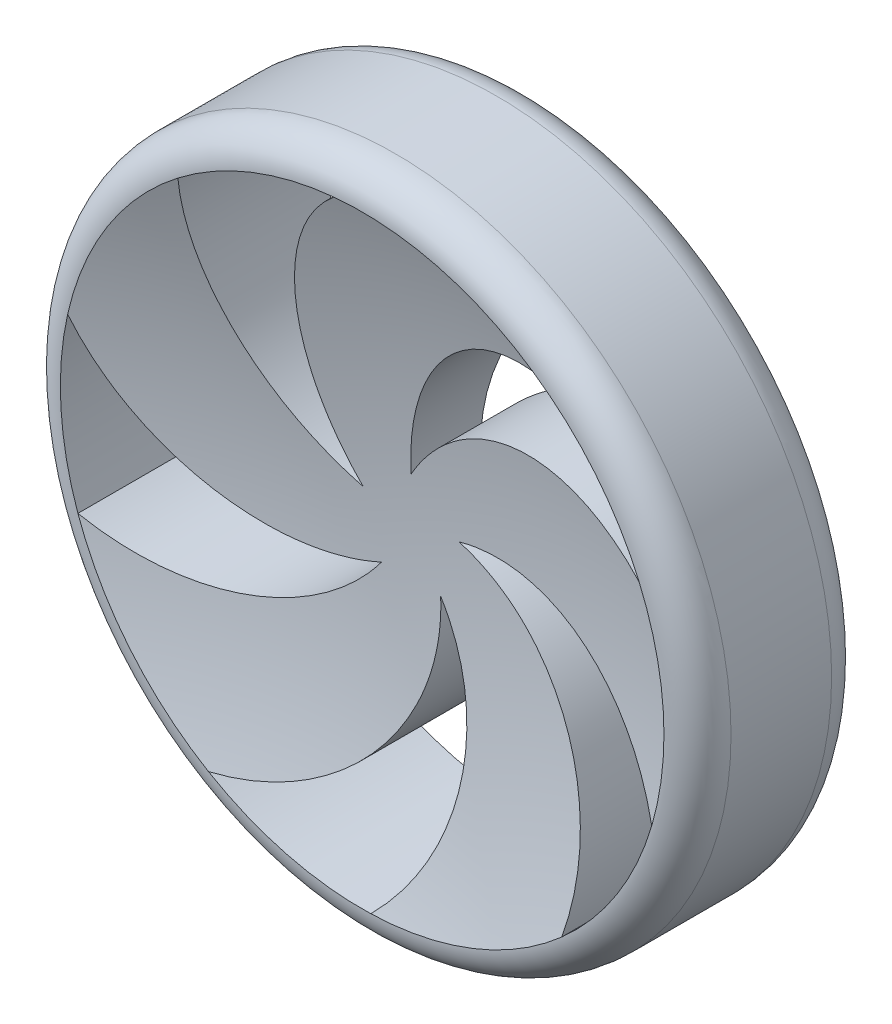
SolidWorks part; units mm, degrees
ref_plane "Front Plane" through (0, 0, 0) normal (0, 0, 1) x (1, 0, 0)
ref_plane "Top Plane" through (0, 0, 0) normal (0, 1, 0) x (1, 0, 0)
ref_plane "Right Plane" through (0, 0, 0) normal (1, 0, 0) x (0, 0, -1)
sketch "Sketch1" plane through (0, 0, 0) normal (0, 0, 1) x (1, 0, 0)
  circle A0 centre (0, 0) radius 100
  dimension "D1" = 200
extrude "Boss-Extrude1" add sketch "Sketch1" along normal blind 50
fillet "Fillet1" radius 10 2 edges at (100, 0, 0) (100, 0, 50)
sketch "Sketch2" plane through (0, 0, 50) normal (0, 0, 1) x (1, 0, 0)
  line L0 (0, 0) -> (0, 90) construction
  circle A0 centre (0, 0) radius 90 construction
  circle A1 centre (0, 0) radius 15 construction
  arc A2 (0, 15) -> (50.8023, 74.2908) centre (60, 15) cw
  arc A3 (0, 15) -> (82.6108, 35.7134) centre (51.5853, -15.6424) cw
  circle A4 centre (0, 0) radius 90
  point P13 (81.2925, 38.6203)
  point P14 (53.8382, -11.4848)
  circle M4 centre (0, 0) radius 90
  dimension "D1" = 30
  dimension "D2" = 60
  dimension "D3" = 60
  dimension "D4" = 50
extrude "Cut-Extrude1" cut sketch "Sketch2" against normal through all contours A2 A3 M4
pattern_circular "CirPattern1" count 5 over 360 about axis through (0, 0, 0) along (0, 0, 1) of "Cut-Extrude1"
sketch "Sketch3" plane through (0, 0, 0) normal (0, 1, 0) x (1, 0, 0)
  line L0 (90, 0) -> (82.6108, 0) construction
  line L1 (90, 0) -> (82.6108, 0) construction
  line L2 (-90, 0) -> (-84.767, 0) construction
  line L3 (-90, 0) -> (-84.767, 0) construction
  line L4 (0, 0) -> (0, -84.8672) construction
  line L5 (0, 0) -> (-90, 0)
  line L6 (-90, 0) -> (-90, -60.0773) construction
  line L7 (0, -50) -> (-90, -50)
  line L8 (-90, -50) -> (-84.767, -50) construction
  line L9 (0, -15) -> (142.267, -15) construction
  line L10 (0, -35) -> (130.6419, -35) construction
  line L11 (0, -15) -> (0, 0)
  line L12 (0, -50) -> (0, -35)
  arc A0 (-90, -50) -> (0, -35) centre (0, -312.5) cw
  arc A1 (-90, 0) -> (0, -15) centre (0, 262.5) ccw
  dimension "D1" = 15
revolve "Cut-Revolve1" cut sketch "Sketch3" angle 360 about L12
